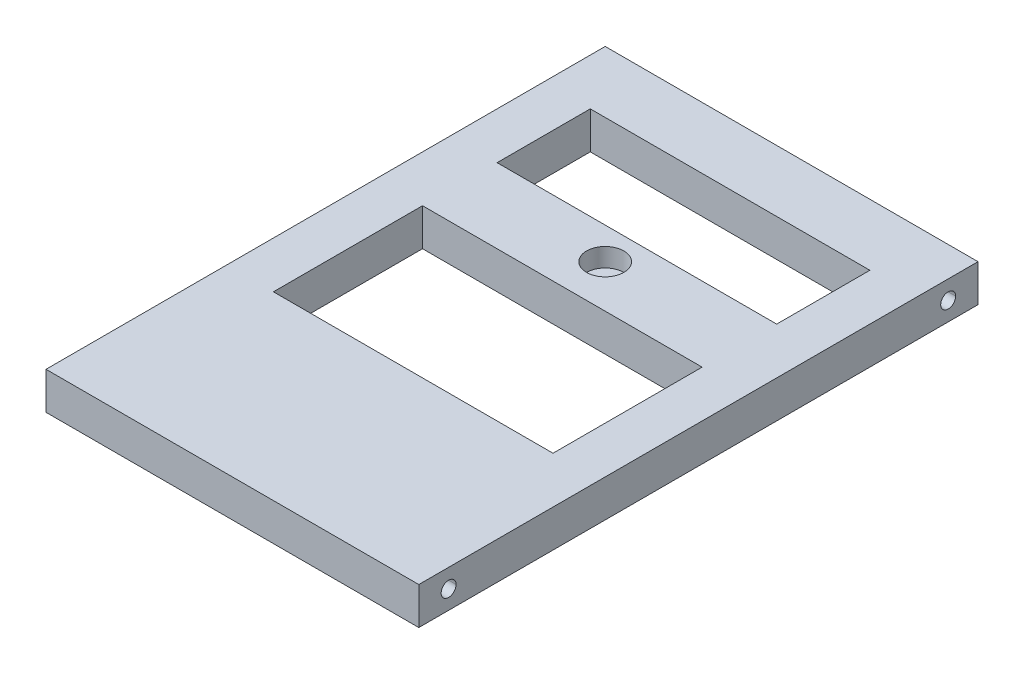
SolidWorks part; units mm, degrees
material "Acrylic (Medium-high impact)"
ref_plane "Front Plane" through (0, 0, 0) normal (0, 0, 1) x (1, 0, 0)
ref_plane "Top Plane" through (0, 0, 0) normal (0, 1, 0) x (1, 0, 0)
ref_plane "Right Plane" through (0, 0, 0) normal (1, 0, 0) x (0, 0, -1)
sketch "Sketch2" plane through (0, 0, 0) normal (0, 1, 0) x (1, 0, 0)
  line L0 (0, 0) -> (0, 150)
  line L1 (0, 150) -> (100, 150)
  line L2 (100, 150) -> (100, 0)
  line L3 (100, 0) -> (0, 0)
  dimension "D1" = 100
  dimension "D2" = 150
extrude "Boss-Extrude1" add sketch "Sketch2" along normal blind 10
sketch "Sketch3" plane through (0, 10, 0) normal (0, 1, 0) x (1, 0, 0)
  line L0 (50, 150) -> (50, 100) construction
  line L1 (100, 150) -> (0, 150) construction
  circle A0 centre (50, 100) radius 5
  dimension "D2" = 10
  dimension "D1" = 50
extrude "MountHole" cut sketch "Sketch3" against normal blind 5
sketch "Sketch4" plane through (0, 0, 0) normal (-1, 0, 0) x (0, 0, 1)
  line L0 (-8, 10) -> (-8, 0) construction
  line L1 (-150, 10) -> (0, 10) construction
  line L2 (-150, 0) -> (0, 0) construction
  line L3 (0, 10) -> (0, 0) construction
  circle A0 centre (-8, 5) radius 2
  dimension "D2" = 4
  dimension "D1" = 8
extrude "Cut-Extrude2" cut sketch "Sketch4" against normal through all
sketch "Sketch5" plane through (0, 0, 0) normal (-1, 0, 0) x (0, 0, 1)
  line L0 (-142, 10) -> (-142, 0) construction
  line L1 (-150, 10) -> (0, 10) construction
  line L2 (-150, 0) -> (0, 0) construction
  line L3 (-150, 10) -> (-150, 0) construction
  circle A0 centre (-142, 5) radius 2
  dimension "D2" = 4
  dimension "D1" = 8
extrude "Cut-Extrude3" cut sketch "Sketch5" against normal through all
fillet "Fillet1" [suppressed] radius 2
sketch "Sketch7" plane through (0, 10, 0) normal (0, 1, 0) x (1, 0, 0)
  line L0 (11, 0) -> (11, 26) construction
  line L1 (0, 0) -> (100, 0) construction
  line L2 (0, 150) -> (0, 0) construction
  line L3 (11, 26) -> (47.1706, 26) construction
  line L9 (11, 26) -> (-5.1328, 26) construction
  line L15 (2.5, 39) -> (2.5, 13)
  line L16 (2.5, 39) -> (30.5, 39)
  line L17 (30.5, 39) -> (30.5, 13)
  line L18 (30.5, 13) -> (2.5, 13)
  point P10 (2.5, 26)
  dimension "D1" = 26
  dimension "D2" = 11
  dimension "D3" = 26
  dimension "D4" = 28
  dimension "D5" = 8.5
extrude "Boss-Extrude2" [suppressed] add sketch "Sketch7" along normal blind 4
sketch "Sketch10" [suppressed] plane through (0, 14, 0) normal (0, 1, 0) x (1, 0, 0)
  line L0 (2.5, 39) -> (2.5, 13)
  line L1 (2.5, 13) -> (3.5, 13)
  line L2 (2.5, 13) -> (30.5, 13) construction
  line L3 (3.5, 13) -> (3.5, 39)
  line L4 (30.5, 39) -> (2.5, 39) construction
  line L5 (3.5, 39) -> (2.5, 39)
  dimension "D1" = 1
extrude "Boss-Extrude3" [suppressed] add sketch "Sketch10" along normal blind 24
sketch "Sketch11" [suppressed] plane through (30.5, 0, 0) normal (1, 0, 0) x (0, 0, -1)
  line L0 (13, 14) -> (39, 14) construction
  line L1 (13, 14) -> (17.3857, 14)
  line L2 (34.6143, 14) -> (39, 14)
  arc A0 (17.3857, 14) -> (34.6143, 14) centre (26, 22.3543) ccw
  dimension "D1" = 12
extrude "Cut-Extrude5" [suppressed] cut sketch "Sketch11" against normal blind 27 and the other way through all
sketch "Sketch13" [suppressed] plane through (2.5, 0, 0) normal (-1, 0, 0) x (0, 0, 1)
  line L0 (-26, 10) -> (-26, 22.354) construction
  line L1 (-39, 10) -> (-13, 10) construction
  line L2 (-26, 22.354) -> (-21.75, 29.7152) construction
  line L3 (-26, 22.354) -> (-6.4369, 22.354) construction
  line L4 (-26, 22.354) -> (-30.25, 29.7152) construction
  circle A0 centre (-26, 22.354) radius 3
  circle A1 centre (-21.75, 29.7152) radius 1
  circle A2 centre (-30.25, 29.7152) radius 1
  dimension "D2" = 6
  dimension "D5" = 2
  dimension "D8" = 2
  dimension "D1" = 12.354
  dimension "D3" = 60
  dimension "D4" = 8.5
  dimension "D6" = 120
  dimension "D7" = 8.5
extrude "Cut-Extrude6" [suppressed] cut sketch "Sketch13" against normal up to surface (1 mm away)
fillet "Fillet2" [suppressed] radius 1
fillet "Fillet3" [suppressed] radius 1
sketch "Sketch14" plane through (0, 10, 0) normal (0, 1, 0) x (1, 0, 0)
  line L0 (50, 0) -> (50, 150) construction
  line L3 (100, 150) -> (0, 150) construction
  line L4 (12.5, 133.5) -> (87.5, 133.5)
  line L5 (12.5, 133.5) -> (12.5, 108.5)
  line L6 (12.5, 108.5) -> (87.5, 108.5)
  line L7 (87.5, 133.5) -> (87.5, 108.5)
  line L8 (12.5, 133.5) -> (87.5, 108.5) construction
  line L9 (12.5, 108.5) -> (87.5, 133.5) construction
  line L10 (12.5, 88.5) -> (87.5, 88.5)
  line L11 (12.5, 88.5) -> (12.5, 48.5)
  line L12 (12.5, 48.5) -> (87.5, 48.5)
  line L13 (87.5, 88.5) -> (87.5, 48.5)
  line L14 (12.5, 88.5) -> (87.5, 48.5) construction
  line L15 (12.5, 48.5) -> (87.5, 88.5) construction
  line L16 (0, 0) -> (100, 0) construction
  point P6 (50, 121)
  point P11 (50, 68.5)
  dimension "D1" = 75
  dimension "D2" = 25
  dimension "D3" = 29
  dimension "D4" = 75
  dimension "D5" = 40
  dimension "D6" = 40
extrude "Cut-Extrude7" cut sketch "Sketch14" against normal through all
sketch "Sketch15" plane through (100, 0, 0) normal (1, 0, 0) x (0, 0, -1)
  line L0 (6, 5) -> (10, 5)
  circle A0 centre (8, 5) radius 2 construction
split line "Split Line1"
sketch "Sketch16" plane through (100, 0, 0) normal (1, 0, 0) x (0, 0, -1)
  line L0 (140, 5) -> (144, 5)
  circle A0 centre (142, 5) radius 2 construction
split line "Split Line2"
fillet "Fillet5" [suppressed] radius 0.5
